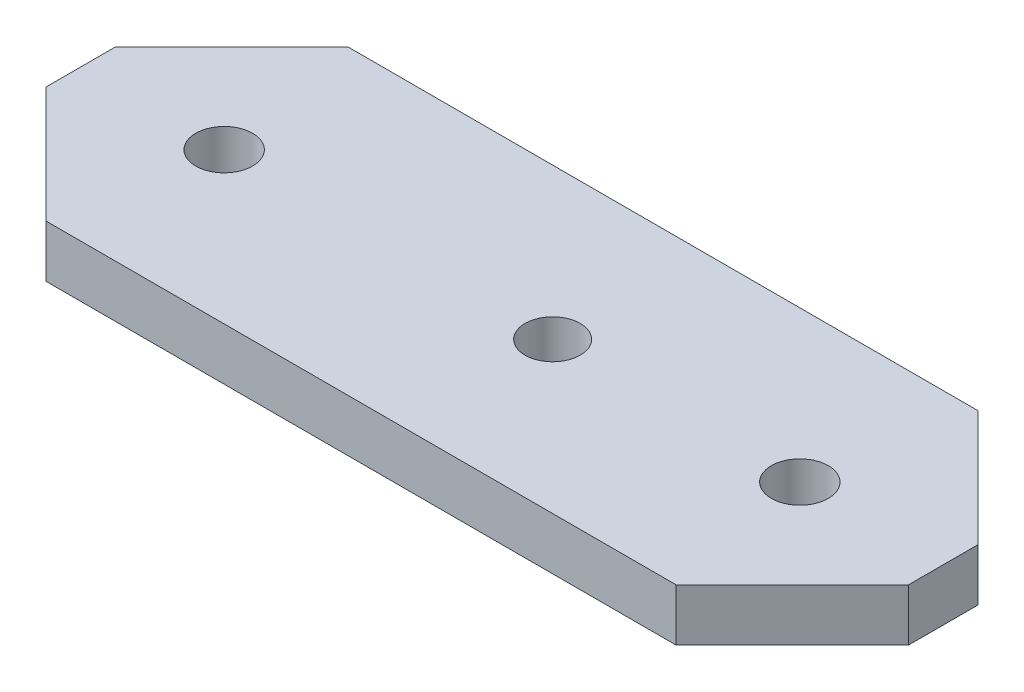
SolidWorks part; units mm, degrees
ref_plane "Front Plane" through (0, 0, 0) normal (0, 0, 1) x (1, 0, 0)
ref_plane "Top Plane" through (0, 0, 0) normal (0, 1, 0) x (1, 0, 0)
ref_plane "Right Plane" through (0, 0, 0) normal (1, 0, 0) x (0, 0, -1)
sketch "Sketch1" plane through (0, 0, 0) normal (0, 1, 0) x (1, 0, 0)
  line L0 (27.15, 26) -> (37.15, 16)
  line L1 (-27.15, 0) -> (27.15, 0)
  line L2 (-27.15, 0) -> (-37.15, 10)
  line L3 (-27.15, 26) -> (27.15, 26)
  line L4 (37.15, 10) -> (37.15, 16)
  line L5 (27.15, 0) -> (37.15, 10)
  line L6 (0, 26) -> (0, 0) construction
  line L7 (-37.15, 10) -> (-37.15, 16)
  line L8 (-27.15, 26) -> (-37.15, 16)
  circle A0 centre (24.8, 13) radius 2.45
  circle A1 centre (-24.8, 13) radius 2.45
  point P1 (37.15, 26)
  point P3 (37.15, 0)
  point P4 (37.15, 13)
  point P18 (-37.15, 0)
  point P19 (-37.15, 26)
  dimension "D3" = 4.9
  dimension "D4" = 12.35
  dimension "D1" = 37.15
  dimension "D2" = 26
extrude "Boss-Extrude1" add sketch "Sketch1" along normal blind 4.5
sketch "Sketch2" plane through (0, 4.5, 0) normal (0, 1, 0) x (1, 0, 0)
  line L0 (37.15, 10) -> (37.15, 16) construction
  circle A0 centre (3.5, 13) radius 2.375
  point P4 (37.15, 13)
  dimension "D1" = 4.75
  dimension "D2" = 33.65
extrude "Cut-Extrude1" cut sketch "Sketch2" against normal through all
